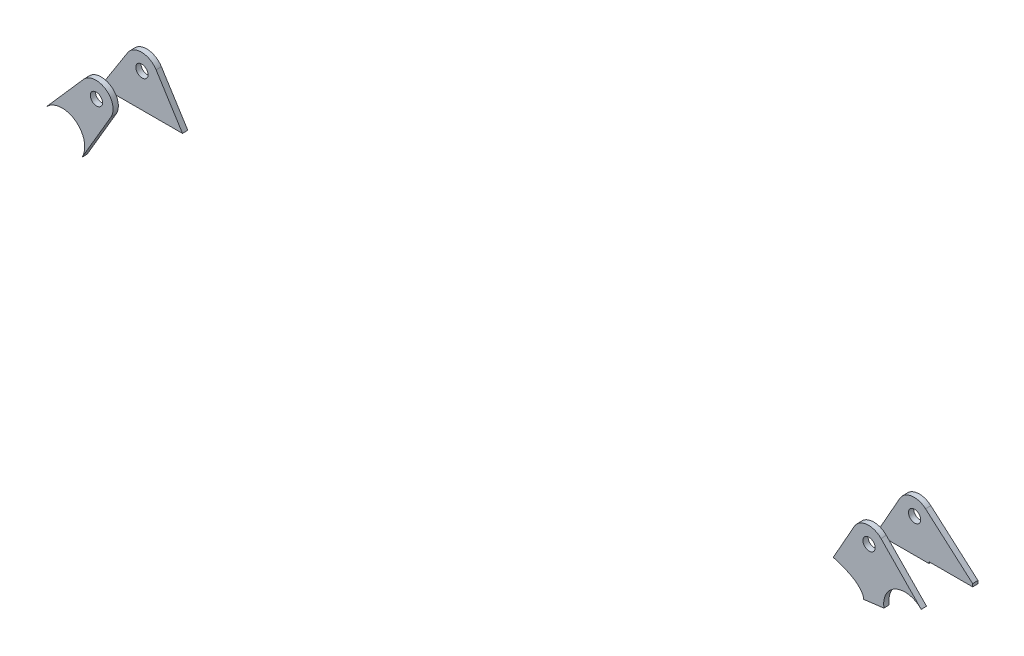
SolidWorks part; units mm, degrees
material "1.0545 (S355N)"
ref_plane "Płaszczyzna XY" through (0, 0, 0) normal (0, 0, 1) x (1, 0, 0)
ref_plane "Płaszczyzna XZ" through (0, 0, 0) normal (0, 1, 0) x (1, 0, 0)
ref_plane "Płaszczyzna YZ" through (0, 0, 0) normal (1, 0, 0) x (0, 0, -1)
ref_plane "Płaszczyzna1" through (0.112, -3.3894, 105.8454) normal (0.0011, -0.032, 0.9995) x (1, 0, -0.0011)
ref_plane "Płaszczyzna2" through (0.1258, -3.8055, 118.8387) normal (0.0011, -0.032, 0.9995) x (1, 0, -0.0011)
sketch "Szkic1" plane through (0.1258, -3.8055, 118.8387) normal (0.0011, -0.032, 0.9995) x (1, 0, -0.0011)
  line L0 (186.9173, 226.8967) -> (209.0509, 202.5512)
  line L1 (171.6608, 225.2562) -> (145.799, 180.4621)
  line L2 (-267.2378, 226.7881) -> (-289.4226, 201.6277)
  line L3 (-251.9658, 215.6177) -> (-269.4622, 186.4548)
  line L4 (179.8881, 220.5062) -> (179.8881, 217.0062) construction
  line L5 (175.8449, 190.7522) -> (187.4892, 192.2424)
  circle A0 centre (179.8881, 220.5062) radius 3.5
  circle A1 centre (-260.1122, 220.5051) radius 3.5
  arc A2 (186.9173, 226.8967) -> (171.6608, 225.2562) centre (179.8881, 220.5062) ccw
  arc A3 (-251.9658, 215.6177) -> (-267.2378, 226.7881) centre (-260.1122, 220.5051) ccw
  circle A4 centre (179.8881, 220.5062) radius 9.5 construction
  circle A5 centre (-260.1122, 220.5051) radius 9.5 construction
  spline S1 degree 3 poles (199.8163, 206.6328) (224.816, 206.7659) (224.9517, 181.2776) (199.952, 181.1445) (174.9524, 181.0114) (174.8167, 206.4998) (199.8163, 206.6328) (224.816, 206.7659) (224.9517, 181.2776) knots -0.5 0 0 0 0.5 0.5 0.5 1 1 1 1.5 1.5 1.5 weights 1 0.333333 0.333333 1 0.333333 0.333333 1 0.333333 0.333333 only from (199.8163, 206.6328) to (199.8163, 206.6328)
  spline S3 degree 3 poles (175.8239, 190.2846) (173.5708, 165.3863) (113.1807, 170.8512) (115.4338, 195.7495) (117.687, 220.6477) (178.0771, 215.1829) (175.8239, 190.2846) (173.5708, 165.3863) (113.1807, 170.8512) knots -0.5 0 0 0 0.5 0.5 0.5 1 1 1 1.5 1.5 1.5 weights 1 0.333333 0.333333 1 0.333333 0.333333 1 0.333333 0.333333 only from (175.8239, 190.2846) to (175.8239, 190.2846)
  spline S5 degree 3 poles (-280.0581, 180.3623) (-305.0577, 180.2292) (-305.1934, 205.7176) (-280.1938, 205.8507) (-255.1941, 205.9838) (-255.0584, 180.4954) (-280.0581, 180.3623) (-305.0577, 180.2292) (-305.1934, 205.7176) knots -0.5 0 0 0 0.5 0.5 0.5 1 1 1 1.5 1.5 1.5 weights 1 0.333333 0.333333 1 0.333333 0.333333 1 0.333333 0.333333 only from (-280.0581, 180.3623) to (-280.0581, 180.3623)
  dimension "D1" = 7
  dimension "D2" = 6
  dimension "D3" = 30
  dimension "D4" = 29
extrude "Dodanie-wyciągnięcie1" add sketch "Szkic1" along normal blind 3 contours L2 S5 L3 A3 A1 | L1 S3 L5 S1 L0 A2 A0
ref_plane "Płaszczyzna3" through (0.0983, -2.9734, 92.852) normal (0.0011, -0.032, 0.9995) x (1, 0, -0.0011)
sketch "Szkic2" plane through (0.0983, -2.9734, 92.852) normal (0.0011, -0.032, 0.9995) x (1, 0, -0.0011)
  line L0 (186.3727, 227.4487) -> (212.4117, 203.1274)
  line L1 (171.6608, 225.2562) -> (157.3902, 200.5387)
  line L2 (-268.0788, 225.6804) -> (-284.3854, 200.5784)
  line L3 (-251.8849, 225.2551) -> (-237.6359, 200.5751)
  line L4 (212.4116, 201.4645) -> (187.4016, 201.4645)
  line L5 (-260.1122, 220.5051) -> (-260.1122, 210.5051) construction
  line L6 (179.8881, 220.5062) -> (179.8881, 217.0062)
  line L7 (171.6608, 225.2562) -> (158.9675, 203.2707) construction
  line L8 (187.4016, 201.4645) -> (187.4016, 200.5387)
  line L9 (187.4016, 200.5387) -> (157.3902, 200.5387)
  line L10 (-237.6359, 200.5751) -> (-284.3854, 200.5784)
  circle A0 centre (-260.1122, 220.5051) radius 3.5 construction
  circle A1 centre (179.8881, 220.5062) radius 3.5 construction
  circle A2 centre (-260.1122, 220.5051) radius 3.5
  circle A3 centre (179.8881, 220.5062) radius 3.5
  arc A4 (-251.8849, 225.2551) -> (-268.0788, 225.6804) centre (-260.1122, 220.5051) ccw
  arc A5 (186.3727, 227.4487) -> (171.6608, 225.2562) centre (179.8881, 220.5062) ccw
  circle A6 centre (179.8881, 220.5062) radius 9.5 construction
  circle A7 centre (-260.1122, 220.5051) radius 9.5 construction
  spline S10 degree 3 poles (212.4117, 203.1274) (212.4117, 202.5731) (212.4116, 202.0188) (212.4116, 201.4645) knots 0 0 0 0 0.72856 0.72856 0.72856 0.72856 weights 1 0.999998 0.999997 0.999998
  dimension "D2" = 30
  dimension "D3" = 33.008
  dimension "D1" = 6
extrude "Dodanie-wyciągnięcie2" add sketch "Szkic2" along normal blind 3 separate body
